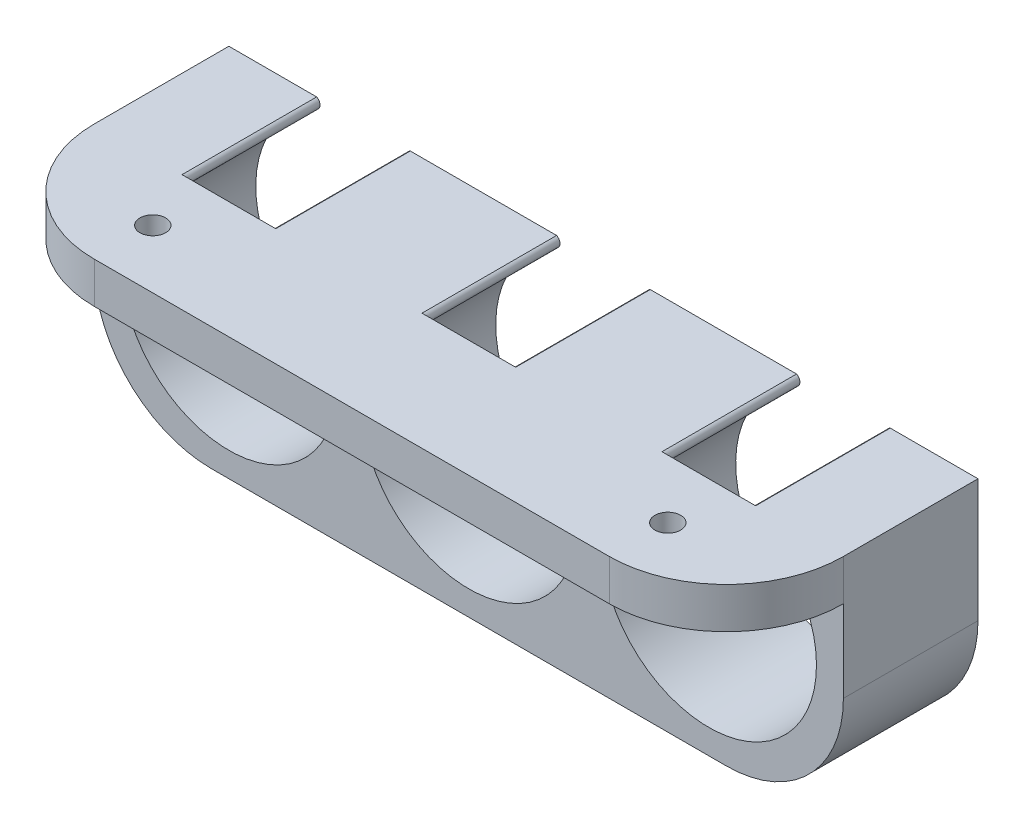
SolidWorks part; units mm, degrees
ref_plane "Plan de face" through (0, 0, 0) normal (0, 0, 1) x (1, 0, 0)
ref_plane "Plan de dessus" through (0, 0, 0) normal (0, 1, 0) x (1, 0, 0)
ref_plane "Plan de droite" through (0, 0, 0) normal (1, 0, 0) x (0, 0, -1)
sketch "Esquisse1" plane through (0, 0, 0) normal (0, 0, 1) x (1, 0, 0)
  line L0 (-24.5, 10.25) -> (-24.5, 9.3349) construction
  line L1 (-32, 10.25) -> (-24.5, 10.25)
  line L2 (-32, 10.25) -> (-32, -0.25)
  line L3 (-22, -10.25) -> (22, -10.25)
  line L4 (32, 10.25) -> (32, -0.25)
  line L5 (-32, 10.25) -> (32, -10.25) construction
  line L6 (-32, -10.25) -> (32, 10.25) construction
  line L7 (-16.5, 10.25) -> (-16.5, 9.3349) construction
  line L8 (-16.5, 10.25) -> (-4, 10.25)
  line L9 (4, 10.25) -> (16.5, 10.25)
  line L10 (24.5, 10.25) -> (32, 10.25)
  arc A1 (-4, 9.3349) -> (4, 9.3349) centre (0, 1.05) ccw
  arc A2 (16.5, 9.3349) -> (24.5, 9.3349) centre (20.5, 1.05) ccw
  arc A3 (-24.5, 9.3349) -> (-16.5, 9.3349) centre (-20.5, 1.05) ccw
  arc A4 (-24.5, 9.3349) -> (-24.5, 10.25) centre (-24.7209, 9.7925) ccw
  arc A5 (-16.5, 9.3349) -> (-16.5, 10.25) centre (-16.2791, 9.7925) cw
  arc A6 (-4, 9.3349) -> (-4, 10.25) centre (-4.2209, 9.7925) ccw
  arc A7 (4, 9.3349) -> (4, 10.25) centre (4.2209, 9.7925) cw
  arc A8 (16.5, 9.3349) -> (16.5, 10.25) centre (16.2791, 9.7925) ccw
  arc A9 (24.5, 9.3349) -> (24.5, 10.25) centre (24.7209, 9.7925) cw
  arc A10 (32, -0.25) -> (22, -10.25) centre (22, -0.25) cw
  arc A11 (-22, -10.25) -> (-32, -0.25) centre (-22, -0.25) cw
  dimension "D3" = 9.2
  dimension "D4" = 20.5
  dimension "D5" = 10
  dimension "D1" = 64
  dimension "D2" = 20.5
  dimension "D8" = 4
  dimension "D9" = 4
  dimension "D10" = 3
extrude "Boss.-Extru.2" add sketch "Esquisse1" along normal blind 11.5
sketch "Esquisse2" plane through (0, 0, 11.5) normal (0, 0, 1) x (1, 0, 0)
  line L0 (32, -0.25) -> (32, 10.25) construction
  line L1 (-32, 10.25) -> (32, 10.25)
  line L2 (-32, 10.25) -> (-32, 6.75)
  line L3 (-32, 6.75) -> (32, 6.75)
  line L4 (32, 10.25) -> (32, 6.75)
  dimension "D1" = 3.5
extrude "Boss.-Extru.3" add sketch "Esquisse2" along normal blind 10
fillet "Congé1" radius 10 2 edges at (32, 8.5, 21.5) (-32, 8.5, 21.5)
sketch "Esquisse3" plane through (0, 6.75, 0) normal (0, -1, 0) x (1, 0, 0)
  line L0 (-22, 21.5) -> (22, 21.5) construction
  circle A0 centre (-22, 16.5) radius 1.1
  circle A1 centre (22, 16.5) radius 1.1
  dimension "D1" = 2.2
  dimension "D2" = 2.2
  dimension "D3" = 5
  dimension "D4" = 44
  dimension "D5" = 22
extrude "Enlèv. mat.-Extru.1" cut sketch "Esquisse3" against normal through all
sketch "Esquisse4" plane through (0, 6.75, 0) normal (0, -1, 0) x (1, 0, 0)
  line L0 (-22, 21.5) -> (22, 21.5) construction
  line L1 (-20.8453, 14.5) -> (-19.6906, 16.5)
  line L2 (-19.6906, 16.5) -> (-20.8453, 18.5)
  line L3 (-20.8453, 18.5) -> (-23.1547, 18.5)
  line L4 (-23.1547, 18.5) -> (-24.3094, 16.5)
  line L5 (-24.3094, 16.5) -> (-23.1547, 14.5)
  line L6 (-23.1547, 14.5) -> (-20.8453, 14.5)
  line L7 (24.3094, 16.5) -> (23.1547, 18.5)
  line L8 (23.1547, 18.5) -> (20.8453, 18.5)
  line L9 (20.8453, 18.5) -> (19.6906, 16.5)
  line L10 (19.6906, 16.5) -> (20.8453, 14.5)
  line L11 (20.8453, 14.5) -> (23.1547, 14.5)
  line L12 (23.1547, 14.5) -> (24.3094, 16.5)
  circle A0 centre (-22, 16.5) radius 2 construction
  circle A1 centre (22, 16.5) radius 2 construction
  dimension "D1" = 4
  dimension "D2" = 4
extrude "Enlèv. mat.-Extru.2" cut sketch "Esquisse4" against normal blind 1.4
